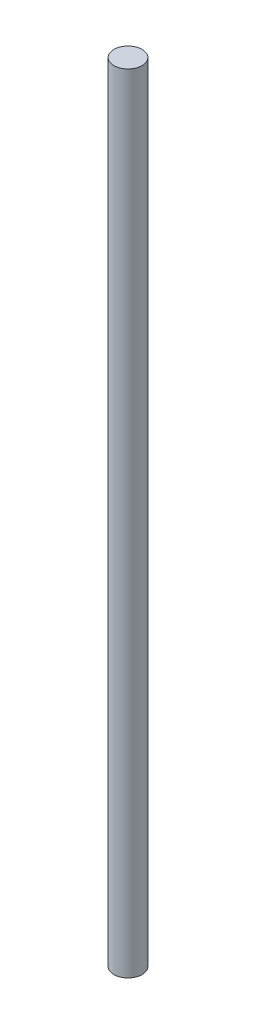
SolidWorks part; units mm, degrees
ref_plane "Front Plane" through (0, 0, 0) normal (0, 0, 1) x (1, 0, 0)
ref_plane "Top Plane" through (0, 0, 0) normal (0, 1, 0) x (1, 0, 0)
ref_plane "Right Plane" through (0, 0, 0) normal (1, 0, 0) x (0, 0, -1)
sketch "Sketch1" plane through (0, 0, 0) normal (0, 1, 0) x (1, 0, 0)
  circle A0 centre (0, 0) radius 1.5
  dimension "D1" = 3
extrude "Boss-Extrude1" add sketch "Sketch1" along normal blind 84
